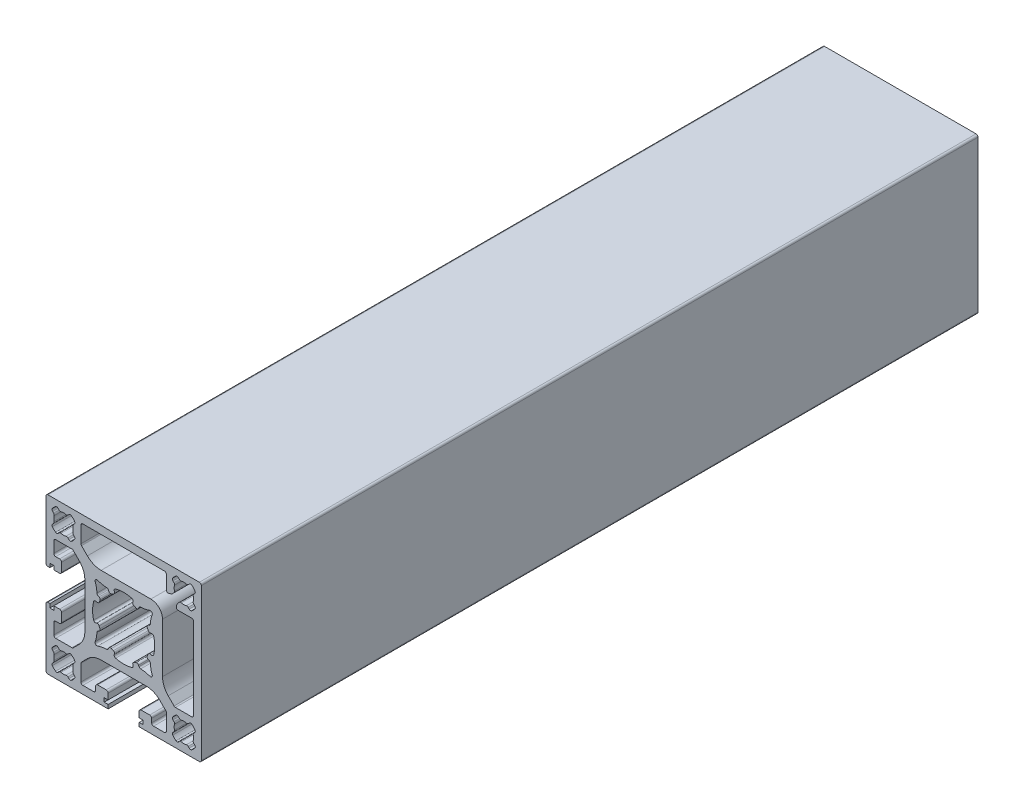
SolidWorks part; units mm, degrees
ref_plane "Front Plane" through (0, 0, 0) normal (0, 0, 1) x (1, 0, 0)
ref_plane "Top Plane" through (0, 0, 0) normal (0, 1, 0) x (1, 0, 0)
ref_plane "Right Plane" through (0, 0, 0) normal (1, 0, 0) x (0, 0, -1)
sketch "Sketch1" plane through (0, 0, 0) normal (0, 0, 1) x (1, 0, 0)
  line L0 (0, -10) -> (0, 10) construction
  line L1 (10, 0) -> (-10, 0) construction
  line L2 (11, 17.5) -> (11, 14.0377)
  line L3 (20, -4.5) -> (20, 4.5)
  line L4 (-10.8536, 12.9749) -> (-9.3431, 11.4645)
  line L5 (-12.9749, 10.8536) -> (-11.4645, 9.3431)
  line L6 (19.5, 20) -> (4, 20)
  line L7 (20, 4.5) -> (20, 19.5)
  line L8 (-3.9555, 6.5896) -> (-3.8287, 6.3177)
  line L9 (-2.3966, 7.0325) -> (-2.3786, 6.9939)
  line L10 (18, -7.7) -> (18, 7.7)
  line L11 (10, 5.8076) -> (10, 7)
  line L12 (7, 10) -> (5.8076, 10)
  line L13 (14.0377, 11) -> (16, 11)
  line L14 (10, -5.8076) -> (10, 5.8076)
  line L15 (-7.043, 2.3972) -> (-6.995, 2.3748)
  line L16 (-6.599, 3.9553) -> (-6.3199, 3.8254)
  line L17 (-14.1155, 18.2988) -> (-14.37, 18.0442)
  line L18 (13.5667, 11.668) -> (13.8354, 12.4212)
  line L19 (-12.7012, 16.8845) -> (-12.9558, 16.63)
  line L20 (-10.5, 18) -> (-7.7, 18)
  line L21 (13.8354, 12.4212) -> (14.1155, 12.7012)
  line L22 (-18.2988, 14.1155) -> (-18.0442, 14.37)
  line L23 (-16.8845, 12.7012) -> (-16.63, 12.9558)
  line L24 (11.668, 13.5667) -> (12.4212, 13.8354)
  line L25 (12.4212, 13.8354) -> (12.7012, 14.1155)
  line L26 (-18.2988, 16.8845) -> (-18.0442, 16.63)
  line L27 (-16.8845, 18.2988) -> (-16.63, 18.0442)
  line L28 (-16.5, 7.2) -> (-17.5, 7.2)
  line L29 (-4, 20) -> (4, 20)
  line L30 (-12.7012, 14.1155) -> (-12.9558, 14.37)
  line L31 (-14.1155, 12.7012) -> (-14.37, 12.9558)
  line L32 (-7.7, 18) -> (7.7, 18)
  line L36 (17.5, 11) -> (16, 11)
  line L37 (-18, 7.7) -> (-18, 10.5)
  line L38 (-17.5, 11) -> (-16, 11)
  line L39 (-19, 4) -> (-19.5, 4)
  line L40 (18, 7.7) -> (18, 10.5)
  line L41 (-19, 4) -> (-19, 5)
  line L42 (-19, 5) -> (-18, 5)
  line L43 (-18, 4) -> (-18, 5)
  line L45 (14.1155, 12.7012) -> (14.37, 12.9558)
  line L46 (12.7012, 14.1155) -> (12.9558, 14.37)
  line L48 (-10, -5.8076) -> (-10, 5.8076)
  line L50 (-13.3284, 11) -> (-16, 11)
  line L51 (-16, 6.7) -> (-16, 4.5)
  line L52 (-16.5, 4) -> (-18, 4)
  line L53 (-20, 4.5) -> (-20, 19.5)
  line L54 (-19.5, 20) -> (-4, 20)
  line L56 (16.8845, 18.2988) -> (16.63, 18.0442)
  line L57 (-11, 17.5) -> (-11, 13.3284)
  line L58 (18.2988, 16.8845) -> (18.0442, 16.63)
  line L59 (-5.8076, 10) -> (5.8076, 10)
  line L62 (16.8845, 12.7012) -> (16.63, 12.9558)
  line L63 (18.2988, 14.1155) -> (18.0442, 14.37)
  line L65 (10.5, 18) -> (7.7, 18)
  line L66 (12.7012, 16.8845) -> (12.9558, 16.63)
  line L67 (14.1155, 18.2988) -> (14.37, 18.0442)
  line L68 (6.599, 3.9553) -> (6.3199, 3.8254)
  line L69 (7.043, 2.3972) -> (6.995, 2.3748)
  line L71 (2.3966, 7.0325) -> (2.3786, 6.9939)
  line L72 (3.9555, 6.5896) -> (3.8287, 6.3177)
  line L75 (10.8536, -12.9749) -> (9.3431, -11.4645)
  line L76 (12.9749, -10.8536) -> (11.4645, -9.3431)
  line L77 (3.9555, -6.5896) -> (3.8287, -6.3177)
  line L78 (2.3966, -7.0325) -> (2.3786, -6.9939)
  line L79 (6.7, -16) -> (4.5, -16)
  line L80 (7.043, -2.3972) -> (6.995, -2.3748)
  line L81 (6.599, -3.9553) -> (6.3199, -3.8254)
  line L82 (14.1155, -18.2988) -> (14.37, -18.0442)
  line L83 (12.7012, -16.8845) -> (12.9558, -16.63)
  line L84 (10.5, -18) -> (7.7, -18)
  line L85 (7.2, -17.5) -> (7.2, -16.5)
  line L86 (18.2988, -14.1155) -> (18.0442, -14.37)
  line L87 (16.8845, -12.7012) -> (16.63, -12.9558)
  line L88 (4, -18) -> (4, -16.5)
  line L89 (4, -19) -> (5, -19)
  line L90 (-5.8076, -10) -> (5.8076, -10)
  line L91 (18.2988, -16.8845) -> (18.0442, -16.63)
  line L92 (-11, -17.5) -> (-11, -13.3284)
  line L93 (16.8845, -18.2988) -> (16.63, -18.0442)
  line L94 (-4, -20) -> (-4, -19)
  line L95 (-19.5, -20) -> (-4, -20)
  line L96 (-20, -4.5) -> (-20, -19.5)
  line L97 (-16.5, -4) -> (-18, -4)
  line L98 (-16, -6.7) -> (-16, -4.5)
  line L99 (-13.3284, -11) -> (-16, -11)
  line L101 (4, -18) -> (5, -18)
  line L102 (12.7012, -14.1155) -> (12.9558, -14.37)
  line L103 (14.1155, -12.7012) -> (14.37, -12.9558)
  line L104 (5, -19) -> (5, -18)
  line L105 (-18, -4) -> (-18, -5)
  line L106 (-19, -5) -> (-18, -5)
  line L107 (-19, -4) -> (-19, -5)
  line L108 (18, -7.7) -> (18, -10.5)
  line L109 (-19, -4) -> (-19.5, -4)
  line L110 (-17.5, -11) -> (-16, -11)
  line L111 (-18, -7.7) -> (-18, -10.5)
  line L112 (17.5, -11) -> (16, -11)
  line L116 (-5, -19) -> (-5, -18)
  line L117 (-14.1155, -12.7012) -> (-14.37, -12.9558)
  line L118 (-12.7012, -14.1155) -> (-12.9558, -14.37)
  line L119 (-4, -18) -> (-5, -18)
  line L120 (-16.5, -7.2) -> (-17.5, -7.2)
  line L121 (-16.8845, -18.2988) -> (-16.63, -18.0442)
  line L122 (-18.2988, -16.8845) -> (-18.0442, -16.63)
  line L123 (-4, -19) -> (-5, -19)
  line L124 (-4, -18) -> (-4, -16.5)
  line L125 (-16.8845, -12.7012) -> (-16.63, -12.9558)
  line L126 (-18.2988, -14.1155) -> (-18.0442, -14.37)
  line L127 (-7.2, -17.5) -> (-7.2, -16.5)
  line L128 (-10.5, -18) -> (-7.7, -18)
  line L129 (-12.7012, -16.8845) -> (-12.9558, -16.63)
  line L131 (-14.1155, -18.2988) -> (-14.37, -18.0442)
  line L132 (-6.599, -3.9553) -> (-6.3199, -3.8254)
  line L133 (-7.043, -2.3972) -> (-6.995, -2.3748)
  line L134 (13.3284, -11) -> (16, -11)
  line L137 (-6.7, -16) -> (-4.5, -16)
  line L138 (-2.3966, -7.0325) -> (-2.3786, -6.9939)
  line L139 (-3.9555, -6.5896) -> (-3.8287, -6.3177)
  line L140 (20, -4.5) -> (20, -19.5)
  line L141 (19.5, -20) -> (4, -20)
  line L142 (-12.9749, -10.8536) -> (-11.4645, -9.3431)
  line L143 (-10.8536, -12.9749) -> (-9.3431, -11.4645)
  line L144 (4, -20) -> (4, -19)
  line L145 (11, -17.5) -> (11, -13.3284)
  arc A0 (2.073, 7.7267) -> (-2.073, 7.7267) centre (0, 0) ccw
  arc A1 (-6.0865, 3.1427) -> (-6.3226, 2.6358) centre (0, 0) ccw
  arc A2 (-6.6942, 7.3368) -> (-4.3944, 6.8781) centre (-4.1945, 13.8752) ccw
  arc A3 (-2.073, 7.7267) -> (-2.3966, 7.0325) centre (-1.9435, 7.2438) ccw
  arc A4 (-7.7369, 2.0733) -> (-7.7369, -2.0733) centre (0, 0) ccw
  arc A5 (-6.8879, 4.3954) -> (-7.3403, 6.6924) centre (-13.8854, 4.2103) ccw
  arc A6 (-17.9148, 16.147) -> (-17.9148, 14.853) centre (-15.5, 15.5) ccw
  arc A7 (-2.3786, 6.9939) -> (-2.6391, 6.3212) centre (-2.8318, 6.7826) cw
  arc A8 (-3.8287, 6.3177) -> (-3.1459, 6.0849) centre (-3.3755, 6.529) ccw
  arc A9 (-2.6391, 6.3212) -> (-3.1459, 6.0849) centre (0, 0) ccw
  arc A10 (-3.9555, 6.5896) -> (-4.3944, 6.8781) centre (-4.4086, 6.3783) ccw
  arc A11 (-6.6942, 7.3368) -> (-7.3403, 6.6924) centre (-6.8728, 6.8697) ccw
  arc A12 (-6.8879, 4.3954) -> (-6.599, 3.9553) centre (-6.3881, 4.4086) ccw
  arc A13 (-6.3199, 3.8254) -> (-6.0865, 3.1427) centre (-6.5308, 3.3721) cw
  arc A14 (-6.995, 2.3748) -> (-6.3226, 2.6358) centre (-6.7841, 2.8282) ccw
  arc A15 (-7.043, 2.3972) -> (-7.7369, 2.0733) centre (-7.254, 1.9438) ccw
  arc A16 (-17.5278, 18.3527) -> (-18.3527, 17.5278) centre (-15.5, 15.5) ccw
  arc A17 (-14.853, 17.9148) -> (-16.147, 17.9148) centre (-15.5, 15.5) ccw
  arc A18 (-13.0852, 14.853) -> (-13.0852, 16.147) centre (-15.5, 15.5) ccw
  arc A19 (-16.147, 13.0852) -> (-14.853, 13.0852) centre (-15.5, 15.5) ccw
  arc A20 (-18.3527, 13.4722) -> (-17.5278, 12.6473) centre (-15.5, 15.5) ccw
  arc A21 (-13.4722, 12.6473) -> (-12.6473, 13.4722) centre (-15.5, 15.5) ccw
  arc A22 (-12.6473, 17.5278) -> (-13.4722, 18.3527) centre (-15.5, 15.5) ccw
  arc A23 (10, 7) -> (7, 10) centre (7, 7) ccw
  arc A24 (14.37, 18.0442) -> (14.853, 17.9148) centre (14.7235, 18.3978) ccw
  arc A25 (14.1155, 18.2988) -> (13.4722, 18.3527) centre (13.7619, 17.9452) ccw
  arc A26 (11.668, 13.5667) -> (11, 14.0377) centre (11.5, 14.0377) cw
  arc A27 (13.5667, 11.668) -> (14.0377, 11) centre (14.0377, 11.5) ccw
  arc A28 (-10.5, 18) -> (-11, 17.5) centre (-10.5, 17.5) ccw
  arc A29 (-9.3431, 11.4645) -> (-5.8076, 10) centre (-5.8076, 15) ccw
  arc A30 (-10, 5.8076) -> (-11.4645, 9.3431) centre (-15, 5.8076) ccw
  arc A31 (-10.8536, 12.9749) -> (-11, 13.3284) centre (-10.5, 13.3284) cw
  arc A32 (-12.9749, 10.8536) -> (-13.3284, 11) centre (-13.3284, 10.5) ccw
  arc A33 (-18, 10.5) -> (-17.5, 11) centre (-17.5, 10.5) cw
  arc A34 (-17.5, 7.2) -> (-18, 7.7) centre (-17.5, 7.7) cw
  arc A35 (-16.5, 7.2) -> (-16, 6.7) centre (-16.5, 6.7) cw
  arc A36 (-16, 4.5) -> (-16.5, 4) centre (-16.5, 4.5) cw
  arc A37 (-19.5, 4) -> (-20, 4.5) centre (-19.5, 4.5) cw
  arc A38 (-20, 19.5) -> (-19.5, 20) centre (-19.5, 19.5) cw
  arc A39 (-16.63, 18.0442) -> (-16.147, 17.9148) centre (-16.2765, 18.3978) ccw
  arc A40 (-17.5278, 18.3527) -> (-16.8845, 18.2988) centre (-17.2381, 17.9452) cw
  arc A41 (-18.2988, 16.8845) -> (-18.3527, 17.5278) centre (-17.9452, 17.2381) cw
  arc A42 (-18.0442, 16.63) -> (-17.9148, 16.147) centre (-18.3978, 16.2765) cw
  arc A43 (-18.0442, 14.37) -> (-17.9148, 14.853) centre (-18.3978, 14.7235) ccw
  arc A44 (-18.2988, 14.1155) -> (-18.3527, 13.4722) centre (-17.9452, 13.7619) ccw
  arc A45 (-17.5278, 12.6473) -> (-16.8845, 12.7012) centre (-17.2381, 13.0548) ccw
  arc A46 (-16.63, 12.9558) -> (-16.147, 13.0852) centre (-16.2765, 12.6022) cw
  arc A47 (-14.37, 12.9558) -> (-14.853, 13.0852) centre (-14.7235, 12.6022) ccw
  arc A48 (-13.4722, 12.6473) -> (-14.1155, 12.7012) centre (-13.7619, 13.0548) cw
  arc A49 (-12.7012, 14.1155) -> (-12.6473, 13.4722) centre (-13.0548, 13.7619) cw
  arc A50 (-12.9558, 14.37) -> (-13.0852, 14.853) centre (-12.6022, 14.7235) cw
  arc A51 (-12.9558, 16.63) -> (-13.0852, 16.147) centre (-12.6022, 16.2765) ccw
  arc A52 (-12.6473, 17.5278) -> (-12.7012, 16.8845) centre (-13.0548, 17.2381) cw
  arc A53 (-14.1155, 18.2988) -> (-13.4722, 18.3527) centre (-13.7619, 17.9452) cw
  arc A54 (-14.37, 18.0442) -> (-14.853, 17.9148) centre (-14.7235, 18.3978) cw
  arc A55 (12.6473, 17.5278) -> (12.7012, 16.8845) centre (13.0548, 17.2381) ccw
  arc A56 (12.9558, 16.63) -> (13.0852, 16.147) centre (12.6022, 16.2765) cw
  arc A57 (12.9558, 14.37) -> (13.0852, 14.853) centre (12.6022, 14.7235) ccw
  arc A60 (14.37, 12.9558) -> (14.853, 13.0852) centre (14.7235, 12.6022) cw
  arc A61 (16.63, 12.9558) -> (16.147, 13.0852) centre (16.2765, 12.6022) ccw
  arc A62 (17.5278, 12.6473) -> (16.8845, 12.7012) centre (17.2381, 13.0548) cw
  arc A63 (18.2988, 14.1155) -> (18.3527, 13.4722) centre (17.9452, 13.7619) cw
  arc A64 (18.0442, 14.37) -> (17.9148, 14.853) centre (18.3978, 14.7235) cw
  arc A65 (18.0442, 16.63) -> (17.9148, 16.147) centre (18.3978, 16.2765) ccw
  arc A66 (18.2988, 16.8845) -> (18.3527, 17.5278) centre (17.9452, 17.2381) ccw
  arc A67 (17.5278, 18.3527) -> (16.8845, 18.2988) centre (17.2381, 17.9452) ccw
  arc A68 (16.63, 18.0442) -> (16.147, 17.9148) centre (16.2765, 18.3978) cw
  arc A69 (20, 19.5) -> (19.5, 20) centre (19.5, 19.5) ccw
  arc A74 (18, 10.5) -> (17.5, 11) centre (17.5, 10.5) ccw
  arc A79 (10.5, 18) -> (11, 17.5) centre (10.5, 17.5) cw
  arc A83 (12.6473, 17.5278) -> (13.4722, 18.3527) centre (15.5, 15.5) cw
  arc A85 (18.3527, 13.4722) -> (17.5278, 12.6473) centre (15.5, 15.5) cw
  arc A86 (16.147, 13.0852) -> (14.853, 13.0852) centre (15.5, 15.5) cw
  arc A87 (13.0852, 14.853) -> (13.0852, 16.147) centre (15.5, 15.5) cw
  arc A88 (14.853, 17.9148) -> (16.147, 17.9148) centre (15.5, 15.5) cw
  arc A89 (17.5278, 18.3527) -> (18.3527, 17.5278) centre (15.5, 15.5) cw
  arc A90 (7.043, 2.3972) -> (7.7369, 2.0733) centre (7.254, 1.9438) cw
  arc A91 (6.995, 2.3748) -> (6.3226, 2.6358) centre (6.7841, 2.8282) cw
  arc A92 (6.3199, 3.8254) -> (6.0865, 3.1427) centre (6.5308, 3.3721) ccw
  arc A93 (6.8879, 4.3954) -> (6.599, 3.9553) centre (6.3881, 4.4086) cw
  arc A94 (6.6942, 7.3368) -> (7.3403, 6.6924) centre (6.8728, 6.8697) cw
  arc A95 (3.9555, 6.5896) -> (4.3944, 6.8781) centre (4.4086, 6.3783) cw
  arc A96 (2.6391, 6.3212) -> (3.1459, 6.0849) centre (0, 0) cw
  arc A97 (3.8287, 6.3177) -> (3.1459, 6.0849) centre (3.3755, 6.529) cw
  arc A98 (2.3786, 6.9939) -> (2.6391, 6.3212) centre (2.8318, 6.7826) ccw
  arc A99 (17.9148, 16.147) -> (17.9148, 14.853) centre (15.5, 15.5) cw
  arc A100 (6.8879, 4.3954) -> (7.3403, 6.6924) centre (13.8854, 4.2103) cw
  arc A101 (7.7369, 2.0733) -> (7.7369, -2.0733) centre (0, 0) cw
  arc A102 (2.073, 7.7267) -> (2.3966, 7.0325) centre (1.9435, 7.2438) cw
  arc A103 (6.6942, 7.3368) -> (4.3944, 6.8781) centre (4.1945, 13.8752) cw
  arc A104 (6.0865, 3.1427) -> (6.3226, 2.6358) centre (0, 0) cw
  arc A105 (6.0865, -3.1427) -> (6.3226, -2.6358) centre (0, 0) ccw
  arc A106 (6.6942, -7.3368) -> (4.3944, -6.8781) centre (4.1945, -13.8752) ccw
  arc A107 (2.073, -7.7267) -> (2.3966, -7.0325) centre (1.9435, -7.2438) ccw
  arc A108 (6.8879, -4.3954) -> (7.3403, -6.6924) centre (13.8854, -4.2103) ccw
  arc A109 (17.9148, -16.147) -> (17.9148, -14.853) centre (15.5, -15.5) ccw
  arc A110 (2.3786, -6.9939) -> (2.6391, -6.3212) centre (2.8318, -6.7826) cw
  arc A111 (3.8287, -6.3177) -> (3.1459, -6.0849) centre (3.3755, -6.529) ccw
  arc A112 (2.6391, -6.3212) -> (3.1459, -6.0849) centre (0, 0) ccw
  arc A113 (3.9555, -6.5896) -> (4.3944, -6.8781) centre (4.4086, -6.3783) ccw
  arc A114 (6.6942, -7.3368) -> (7.3403, -6.6924) centre (6.8728, -6.8697) ccw
  arc A115 (6.8879, -4.3954) -> (6.599, -3.9553) centre (6.3881, -4.4086) ccw
  arc A116 (6.3199, -3.8254) -> (6.0865, -3.1427) centre (6.5308, -3.3721) cw
  arc A117 (6.995, -2.3748) -> (6.3226, -2.6358) centre (6.7841, -2.8282) ccw
  arc A118 (7.043, -2.3972) -> (7.7369, -2.0733) centre (7.254, -1.9438) ccw
  arc A119 (17.5278, -18.3527) -> (18.3527, -17.5278) centre (15.5, -15.5) ccw
  arc A120 (14.853, -17.9148) -> (16.147, -17.9148) centre (15.5, -15.5) ccw
  arc A121 (13.0852, -14.853) -> (13.0852, -16.147) centre (15.5, -15.5) ccw
  arc A122 (16.147, -13.0852) -> (14.853, -13.0852) centre (15.5, -15.5) ccw
  arc A123 (18.3527, -13.4722) -> (17.5278, -12.6473) centre (15.5, -15.5) ccw
  arc A124 (13.4722, -12.6473) -> (12.6473, -13.4722) centre (15.5, -15.5) ccw
  arc A125 (12.6473, -17.5278) -> (13.4722, -18.3527) centre (15.5, -15.5) ccw
  arc A126 (4, -16.5) -> (4.5, -16) centre (4.5, -16.5) cw
  arc A127 (7.2, -16.5) -> (6.7, -16) centre (6.7, -16.5) ccw
  arc A128 (7.7, -18) -> (7.2, -17.5) centre (7.7, -17.5) cw
  arc A129 (10.5, -18) -> (11, -17.5) centre (10.5, -17.5) ccw
  arc A130 (9.3431, -11.4645) -> (5.8076, -10) centre (5.8076, -15) ccw
  arc A131 (10, -5.8076) -> (11.4645, -9.3431) centre (15, -5.8076) ccw
  arc A132 (10.8536, -12.9749) -> (11, -13.3284) centre (10.5, -13.3284) cw
  arc A133 (12.9749, -10.8536) -> (13.3284, -11) centre (13.3284, -10.5) ccw
  arc A134 (18, -10.5) -> (17.5, -11) centre (17.5, -10.5) cw
  arc A139 (20, -19.5) -> (19.5, -20) centre (19.5, -19.5) cw
  arc A140 (16.63, -18.0442) -> (16.147, -17.9148) centre (16.2765, -18.3978) ccw
  arc A141 (17.5278, -18.3527) -> (16.8845, -18.2988) centre (17.2381, -17.9452) cw
  arc A142 (18.2988, -16.8845) -> (18.3527, -17.5278) centre (17.9452, -17.2381) cw
  arc A143 (18.0442, -16.63) -> (17.9148, -16.147) centre (18.3978, -16.2765) cw
  arc A144 (18.0442, -14.37) -> (17.9148, -14.853) centre (18.3978, -14.7235) ccw
  arc A145 (18.2988, -14.1155) -> (18.3527, -13.4722) centre (17.9452, -13.7619) ccw
  arc A146 (17.5278, -12.6473) -> (16.8845, -12.7012) centre (17.2381, -13.0548) ccw
  arc A147 (16.63, -12.9558) -> (16.147, -13.0852) centre (16.2765, -12.6022) cw
  arc A148 (14.37, -12.9558) -> (14.853, -13.0852) centre (14.7235, -12.6022) ccw
  arc A149 (13.4722, -12.6473) -> (14.1155, -12.7012) centre (13.7619, -13.0548) cw
  arc A150 (12.7012, -14.1155) -> (12.6473, -13.4722) centre (13.0548, -13.7619) cw
  arc A151 (12.9558, -14.37) -> (13.0852, -14.853) centre (12.6022, -14.7235) cw
  arc A152 (12.9558, -16.63) -> (13.0852, -16.147) centre (12.6022, -16.2765) ccw
  arc A153 (12.6473, -17.5278) -> (12.7012, -16.8845) centre (13.0548, -17.2381) cw
  arc A154 (-14.37, -18.0442) -> (-14.853, -17.9148) centre (-14.7235, -18.3978) ccw
  arc A155 (-14.1155, -18.2988) -> (-13.4722, -18.3527) centre (-13.7619, -17.9452) ccw
  arc A156 (-12.6473, -17.5278) -> (-12.7012, -16.8845) centre (-13.0548, -17.2381) ccw
  arc A157 (-12.9558, -16.63) -> (-13.0852, -16.147) centre (-12.6022, -16.2765) cw
  arc A158 (-12.9558, -14.37) -> (-13.0852, -14.853) centre (-12.6022, -14.7235) ccw
  arc A159 (-12.7012, -14.1155) -> (-12.6473, -13.4722) centre (-13.0548, -13.7619) ccw
  arc A160 (-13.4722, -12.6473) -> (-14.1155, -12.7012) centre (-13.7619, -13.0548) ccw
  arc A161 (-14.37, -12.9558) -> (-14.853, -13.0852) centre (-14.7235, -12.6022) cw
  arc A162 (-16.63, -12.9558) -> (-16.147, -13.0852) centre (-16.2765, -12.6022) ccw
  arc A163 (-17.5278, -12.6473) -> (-16.8845, -12.7012) centre (-17.2381, -13.0548) cw
  arc A164 (-18.2988, -14.1155) -> (-18.3527, -13.4722) centre (-17.9452, -13.7619) cw
  arc A165 (-18.0442, -14.37) -> (-17.9148, -14.853) centre (-18.3978, -14.7235) cw
  arc A166 (-18.0442, -16.63) -> (-17.9148, -16.147) centre (-18.3978, -16.2765) ccw
  arc A167 (-18.2988, -16.8845) -> (-18.3527, -17.5278) centre (-17.9452, -17.2381) ccw
  arc A168 (-17.5278, -18.3527) -> (-16.8845, -18.2988) centre (-17.2381, -17.9452) ccw
  arc A169 (-16.63, -18.0442) -> (-16.147, -17.9148) centre (-16.2765, -18.3978) cw
  arc A170 (-20, -19.5) -> (-19.5, -20) centre (-19.5, -19.5) ccw
  arc A171 (-19.5, -4) -> (-20, -4.5) centre (-19.5, -4.5) ccw
  arc A172 (-16, -4.5) -> (-16.5, -4) centre (-16.5, -4.5) ccw
  arc A173 (-16.5, -7.2) -> (-16, -6.7) centre (-16.5, -6.7) ccw
  arc A174 (-17.5, -7.2) -> (-18, -7.7) centre (-17.5, -7.7) ccw
  arc A175 (-18, -10.5) -> (-17.5, -11) centre (-17.5, -10.5) ccw
  arc A176 (-12.9749, -10.8536) -> (-13.3284, -11) centre (-13.3284, -10.5) cw
  arc A177 (-10.8536, -12.9749) -> (-11, -13.3284) centre (-10.5, -13.3284) ccw
  arc A178 (-10, -5.8076) -> (-11.4645, -9.3431) centre (-15, -5.8076) cw
  arc A179 (-9.3431, -11.4645) -> (-5.8076, -10) centre (-5.8076, -15) cw
  arc A180 (-10.5, -18) -> (-11, -17.5) centre (-10.5, -17.5) cw
  arc A181 (-7.7, -18) -> (-7.2, -17.5) centre (-7.7, -17.5) ccw
  arc A182 (-7.2, -16.5) -> (-6.7, -16) centre (-6.7, -16.5) cw
  arc A183 (14.1155, -18.2988) -> (13.4722, -18.3527) centre (13.7619, -17.9452) cw
  arc A184 (14.37, -18.0442) -> (14.853, -17.9148) centre (14.7235, -18.3978) cw
  arc A185 (-4, -16.5) -> (-4.5, -16) centre (-4.5, -16.5) ccw
  arc A186 (-12.6473, -17.5278) -> (-13.4722, -18.3527) centre (-15.5, -15.5) cw
  arc A187 (-13.4722, -12.6473) -> (-12.6473, -13.4722) centre (-15.5, -15.5) cw
  arc A188 (-18.3527, -13.4722) -> (-17.5278, -12.6473) centre (-15.5, -15.5) cw
  arc A189 (-16.147, -13.0852) -> (-14.853, -13.0852) centre (-15.5, -15.5) cw
  arc A190 (-13.0852, -14.853) -> (-13.0852, -16.147) centre (-15.5, -15.5) cw
  arc A191 (-14.853, -17.9148) -> (-16.147, -17.9148) centre (-15.5, -15.5) cw
  arc A192 (-17.5278, -18.3527) -> (-18.3527, -17.5278) centre (-15.5, -15.5) cw
  arc A193 (-7.043, -2.3972) -> (-7.7369, -2.0733) centre (-7.254, -1.9438) cw
  arc A194 (-6.995, -2.3748) -> (-6.3226, -2.6358) centre (-6.7841, -2.8282) cw
  arc A195 (-6.3199, -3.8254) -> (-6.0865, -3.1427) centre (-6.5308, -3.3721) ccw
  arc A196 (-6.8879, -4.3954) -> (-6.599, -3.9553) centre (-6.3881, -4.4086) cw
  arc A197 (-6.6942, -7.3368) -> (-7.3403, -6.6924) centre (-6.8728, -6.8697) cw
  arc A198 (-3.9555, -6.5896) -> (-4.3944, -6.8781) centre (-4.4086, -6.3783) cw
  arc A199 (-2.6391, -6.3212) -> (-3.1459, -6.0849) centre (0, 0) cw
  arc A200 (-3.8287, -6.3177) -> (-3.1459, -6.0849) centre (-3.3755, -6.529) cw
  arc A201 (-2.3786, -6.9939) -> (-2.6391, -6.3212) centre (-2.8318, -6.7826) ccw
  arc A202 (-17.9148, -16.147) -> (-17.9148, -14.853) centre (-15.5, -15.5) cw
  arc A203 (-6.8879, -4.3954) -> (-7.3403, -6.6924) centre (-13.8854, -4.2103) cw
  arc A204 (-2.073, -7.7267) -> (-2.3966, -7.0325) centre (-1.9435, -7.2438) cw
  arc A205 (-6.6942, -7.3368) -> (-4.3944, -6.8781) centre (-4.1945, -13.8752) cw
  arc A206 (-6.0865, -3.1427) -> (-6.3226, -2.6358) centre (0, 0) cw
  arc A207 (2.073, -7.7267) -> (-2.073, -7.7267) centre (0, 0) cw
  point P46 (-4.089, 6.876)
  point P49 (-8, 8)
  point P54 (-5.8294, 3.5972)
  point P98 (11, 13.3284)
  point P102 (-4, 19)
  point P104 (13.3284, 11)
  point P137 (-18.5788, 13.8354)
  point P140 (-17.1646, 12.4212)
  point P143 (-16.4131, 13.1727)
  point P148 (-13.8354, 12.4212)
  point P151 (-12.4212, 13.8354)
  point P158 (-12.4212, 17.1646)
  point P161 (-13.8354, 18.5788)
  point P277 (13.8354, 18.5788)
  point P278 (12.4212, 17.1646)
  point P279 (12.4212, 13.8354)
  point P280 (13.8354, 12.4212)
  point P281 (16.4131, 13.1727)
  point P282 (17.1646, 12.4212)
  point P283 (18.5788, 13.8354)
  point P284 (5.8294, 3.5972)
  point P285 (8, 8)
  point P286 (4.089, 6.876)
  point P546 (4.089, -6.876)
  point P547 (8, -8)
  point P548 (5.8294, -3.5972)
  point P549 (18.5788, -13.8354)
  point P550 (17.1646, -12.4212)
  point P551 (16.4131, -13.1727)
  point P552 (13.8354, -12.4212)
  point P553 (12.4212, -13.8354)
  point P554 (12.4212, -17.1646)
  point P555 (13.8354, -18.5788)
  point P556 (-13.8354, -18.5788)
  point P557 (-12.4212, -17.1646)
  point P558 (-12.4212, -13.8354)
  point P559 (-13.8354, -12.4212)
  point P560 (-16.4131, -13.1727)
  point P561 (-17.1646, -12.4212)
  point P562 (-18.5788, -13.8354)
  point P563 (-5.8294, -3.5972)
  point P564 (-8, -8)
  point P565 (-4.089, -6.876)
extrude "Extrude1" add sketch "Sketch1" against normal blind 200
